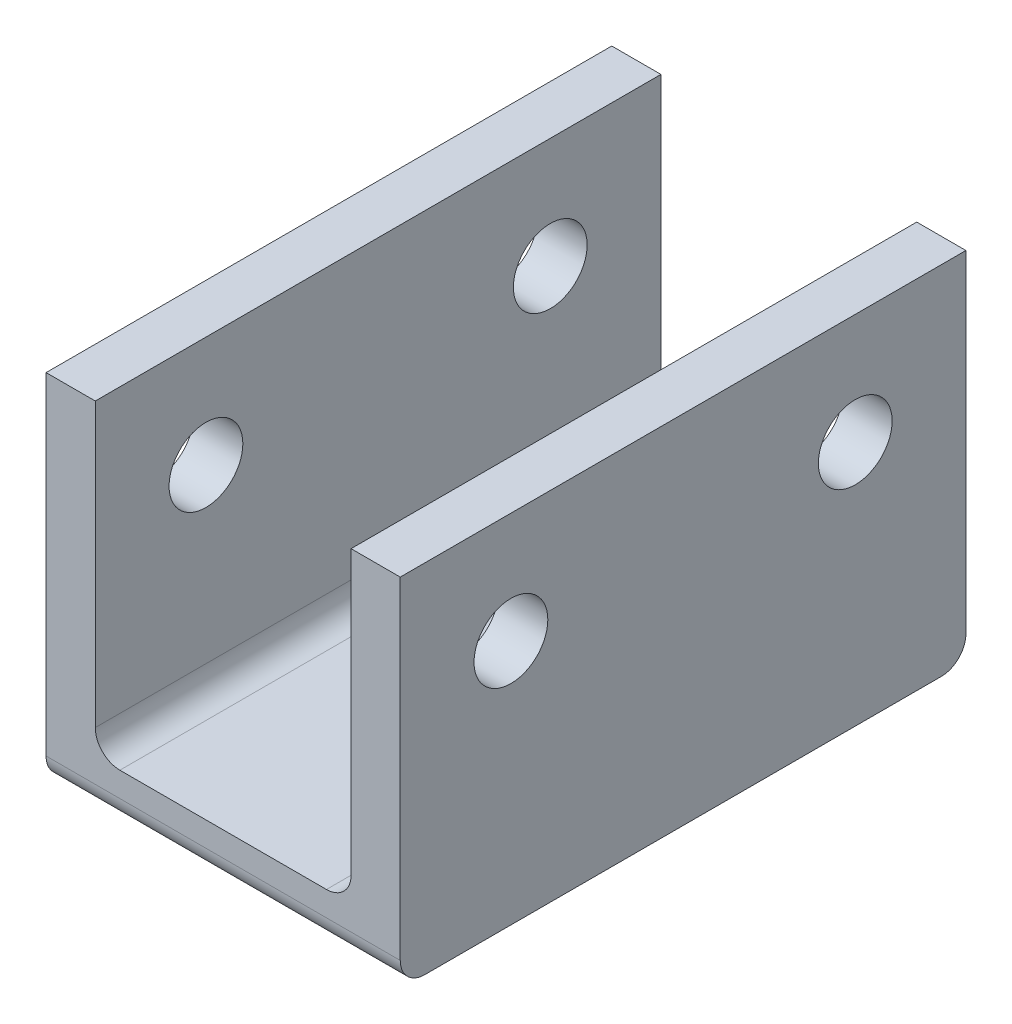
SolidWorks part; units mm, degrees
ref_plane "Front Plane" through (0, 0, 0) normal (0, 0, 1) x (1, 0, 0)
ref_plane "Top Plane" through (0, 0, 0) normal (0, 1, 0) x (1, 0, 0)
ref_plane "Right Plane" through (0, 0, 0) normal (1, 0, 0) x (0, 0, -1)
sketch "Sketch1" plane through (0, 0, 0) normal (0, 0, 1) x (1, 0, 0)
  line L0 (-5.2, 1) -> (5.2, 1)
  line L5 (7.2, -1) -> (-7.2, -1)
  line L6 (-5.2, 1) -> (-5.2, 13.5)
  line L7 (-5.2, 13.5) -> (-7.2, 13.5)
  line L8 (-7.2, 13.5) -> (-7.2, -1)
  line L9 (0, -55) -> (0, 55) construction
  line L10 (7.2, 13.5) -> (7.2, -1)
  line L11 (5.2, 13.5) -> (7.2, 13.5)
  line L12 (5.2, 1) -> (5.2, 13.5)
  point P2 (0, 1)
  point P4 (0, 0)
  point P5 (-3.2311, -1)
  point P10 (0, 0)
  point P16 (0, -1)
  dimension "D1" = 1
  dimension "D2" = 1
  dimension "D3" = 2
  dimension "D4" = 14.4
  dimension "D5" = 13.5
extrude "Boss-Extrude1" add sketch "Sketch1" along normal mid plane 23
sketch "Sketch2" plane through (7.2, 0, 0) normal (1, 0, 0) x (0, 0, -1)
  line L0 (0, 7.92) -> (0, -7.92) construction
  line L1 (-11.5, 13.5) -> (11.5, 13.5) construction
  circle A0 centre (-7, 9) radius 1.5
  circle A1 centre (7, 9) radius 1.5
  dimension "D3" = 3
  dimension "D1" = 14
  dimension "D2" = 4.5
extrude "Cut-Extrude1" cut sketch "Sketch2" against normal through all both and the other way through all
fillet "Fillet1" radius 1 2 edges at (0, -1, 11.5) (0, -1, -11.5)
fillet "Fillet2" radius 1 2 edges at (-5.2, 1, 0) (5.2, 1, 0)
